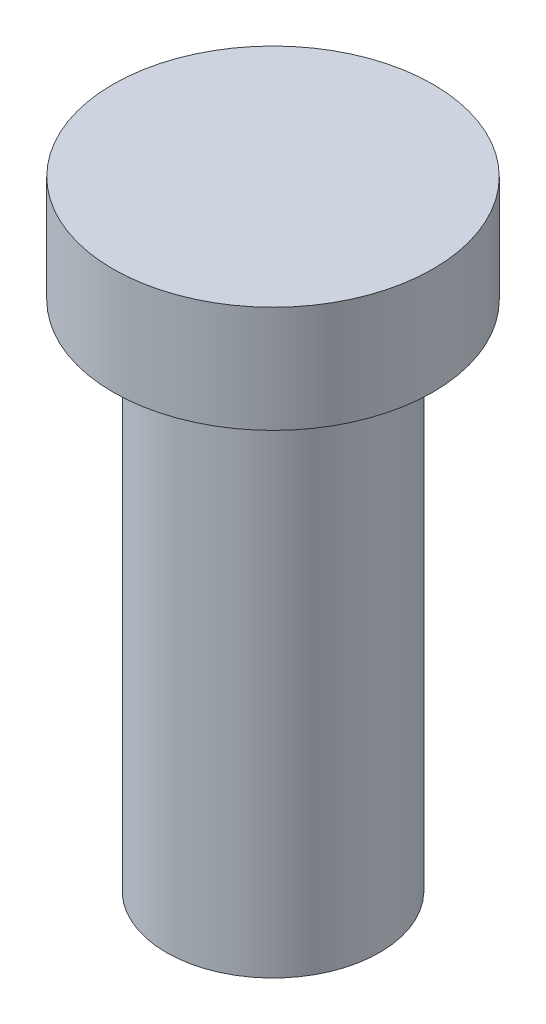
SolidWorks part; units mm, degrees
ref_plane "Front Plane" through (0, 0, 0) normal (0, 0, 1) x (1, 0, 0)
ref_plane "Top Plane" through (0, 0, 0) normal (0, 1, 0) x (1, 0, 0)
ref_plane "Right Plane" through (0, 0, 0) normal (1, 0, 0) x (0, 0, -1)
sketch "Sketch1" plane through (0, 0, 0) normal (0, 1, 0) x (1, 0, 0)
  circle A0 centre (0, 0) radius 2.5
  dimension "D1" = 5
extrude "Boss-Extrude1" add sketch "Sketch1" along normal blind 12
sketch "Sketch2" plane through (0, 12, 0) normal (0, 1, 0) x (1, 0, 0)
  circle A0 centre (0, 0) radius 3.75
extrude "Boss-Extrude2" add sketch "Sketch2" along normal blind 2.5
